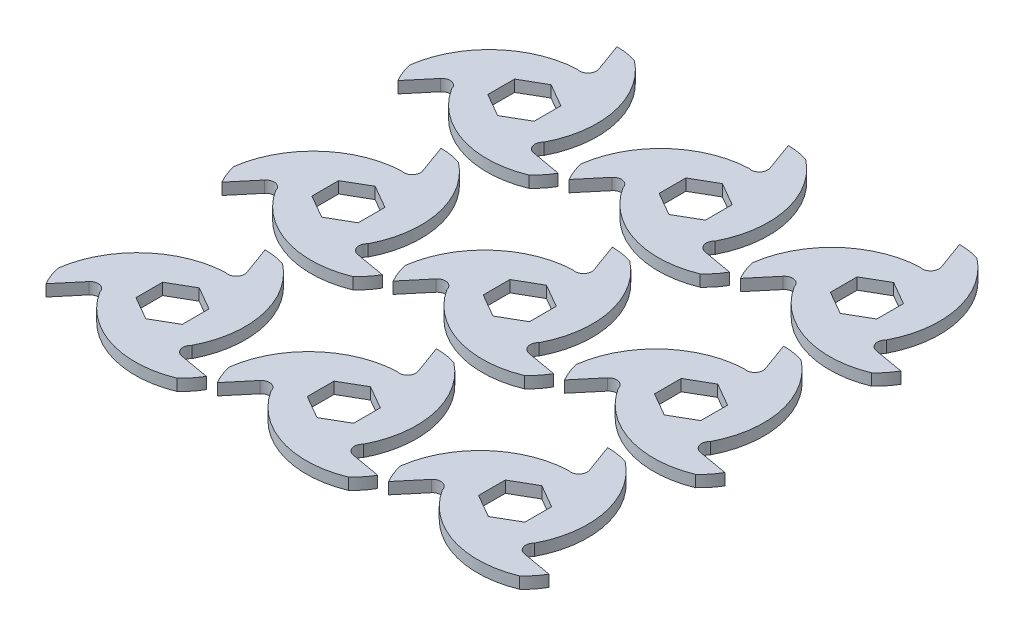
SolidWorks part; units mm, degrees
ref_plane "Front Plane" through (0, 0, 0) normal (0, 0, 1) x (1, 0, 0)
ref_plane "Top Plane" through (0, 0, 0) normal (0, 1, 0) x (1, 0, 0)
ref_plane "Right Plane" through (0, 0, 0) normal (1, 0, 0) x (0, 0, -1)
sketch "Sketch2" plane through (0, 0, 0) normal (0, 1, 0) x (1, 0, 0)
  line L0 (0, 50.8) -> (0, 0) construction
  line L1 (0, 0) -> (-43.9941, -25.4) construction
  line L2 (0, 0) -> (43.9941, -25.4) construction
  line L3 (0, 50.8) -> (5.6992, 35.1416)
  line L4 (43.9941, -25.4) -> (27.5839, -22.5064)
  line L5 (-43.9941, -25.4) -> (-33.2831, -12.6352)
  line L7 (0, 14.6647) -> (-12.7, 7.3323)
  line L8 (-12.7, 7.3323) -> (-12.7, -7.3323)
  line L9 (-12.7, -7.3323) -> (0, -14.6647)
  line L10 (0, -14.6647) -> (12.7, -7.3323)
  line L11 (12.7, -7.3323) -> (12.7, 7.3323)
  line L12 (12.7, 7.3323) -> (0, 14.6647)
  circle A0 centre (0, 0) radius 50.8 construction
  circle A1 centre (0, 13.2055) radius 37.5945
  circle A2 centre (11.4363, -6.6028) radius 37.5945
  circle A3 centre (-11.4363, -6.6028) radius 37.5945
  arc A4 (5.6992, 35.1416) -> (0, 29.21) centre (1.3938, 33.5746) cw
  arc A5 (27.5839, -22.5064) -> (25.2966, -14.605) centre (28.3796, -17.9943) cw
  arc A6 (-33.2831, -12.6352) -> (-25.2966, -14.605) centre (-29.7733, -15.5803) cw
  circle A7 centre (0, 0) radius 12.7 construction
  point P25 (0, 0)
  dimension "D1" = 101.6
  dimension "D4" = 20
  dimension "D2" = 120
  dimension "D3" = 120
  dimension "D5" = 21.59
  dimension "D8" = 25.4
  dimension "D7" = 3
extrude "Boss-Extrude2" add sketch "Sketch2" along normal mid plane 6.35 contours A1 A3 A2 L12 L11 L10 L9 L8 L7 | A1 A6 A2 A3 | L5 A6 A1 A3 | L4 A5 A3 A2 | A3 A5 A1 A2 | A2 A4 A3 A1 | L3 A4 A2 A1
sketch "Sketch3" plane through (0, 3.175, 0) normal (0, 1, 0) x (1, 0, 0)
  line L3 (43.9941, -25.4) -> (27.5839, -22.5064)
  line L4 (0, 50.8) -> (5.6992, 35.1416)
  line L5 (-43.9941, -25.4) -> (-33.2831, -12.6352)
  line L6 (43.9941, -25.4) -> (27.5839, -22.5064)
  line L7 (0, 50.8) -> (5.6992, 35.1416)
  line L8 (-43.9941, -25.4) -> (-33.2831, -12.6352)
  arc A0 (-48.1379, -14.7476) -> (0, 29.21) centre (2.2057, -21.5421) cw
  arc A1 (0, 29.21) -> (-43.9941, -25.4) centre (-11.4363, -6.6028) ccw construction
  arc A2 (0, 29.21) -> (5.6992, 35.1416) centre (1.3938, 33.5746) ccw construction
  arc A3 (11.2972, 49.0624) -> (25.2966, -14.605) centre (-19.7588, 8.8609) cw
  arc A4 (36.8407, -34.3148) -> (-25.2966, -14.605) centre (17.5532, 12.6812) cw
  arc A9 (-25.2966, -14.605) -> (-33.2831, -12.6352) centre (-29.7733, -15.5803) ccw
  arc A10 (-25.2966, -14.605) -> (43.9941, -25.4) centre (11.4363, -6.6028) ccw
  arc A11 (25.2966, -14.605) -> (27.5839, -22.5064) centre (28.3796, -17.9943) ccw
  arc A12 (25.2966, -14.605) -> (0, 50.8) centre (0, 13.2055) ccw
  arc A13 (0, 29.21) -> (5.6992, 35.1416) centre (1.3938, 33.5746) ccw
  arc A14 (0, 29.21) -> (-43.9941, -25.4) centre (-11.4363, -6.6028) ccw
  arc A15 (-25.2966, -14.605) -> (-33.2831, -12.6352) centre (-29.7733, -15.5803) ccw
  arc A16 (-25.2966, -14.605) -> (43.9941, -25.4) centre (11.4363, -6.6028) ccw
  arc A17 (25.2966, -14.605) -> (27.5839, -22.5064) centre (28.3796, -17.9943) ccw
  arc A18 (25.2966, -14.605) -> (0, 50.8) centre (0, 13.2055) ccw
  arc A19 (0, 29.21) -> (5.6992, 35.1416) centre (1.3938, 33.5746) ccw
  arc A20 (0, 29.21) -> (-43.9941, -25.4) centre (-11.4363, -6.6028) ccw
  point P26 (0, 0)
  arc M20 (-25.2966, -14.605) -> (43.9941, -25.4) centre (11.4363, -6.6028) ccw
  arc M23 (25.2966, -14.605) -> (0, 50.8) centre (0, 13.2055) ccw
  arc M26 (0, 29.21) -> (-43.9941, -25.4) centre (-11.4363, -6.6028) ccw
  dimension "D3" = 50.8
  dimension "D1" = 11.43
  dimension "D2" = 0
  dimension "D4" = 3
extrude "Cut-Extrude1" cut sketch "Sketch3" against normal through all contours A0 M26 | A3 M23 | A4 M20
pattern_linear "LPattern1" count 3 spacing 96.52 along (0, 0, 1) count 3 spacing 93.98 along (1, 0, 0) of "Boss-Extrude2"
